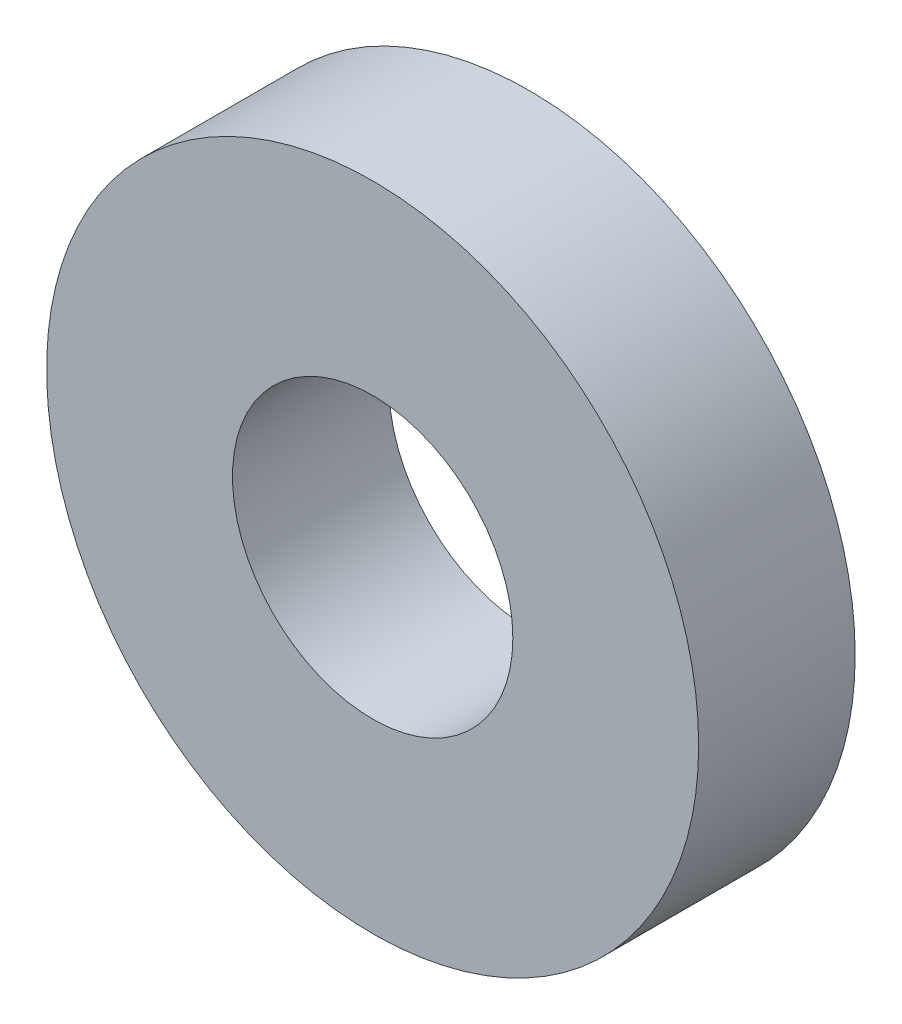
SolidWorks part; units mm, degrees
ref_plane "Front Plane" through (0, 0, 0) normal (0, 0, 1) x (1, 0, 0)
ref_plane "Top Plane" through (0, 0, 0) normal (0, 1, 0) x (1, 0, 0)
ref_plane "Right Plane" through (0, 0, 0) normal (1, 0, 0) x (0, 0, -1)
sketch "Sketch1" plane through (0, 0, 0) normal (0, 0, 1) x (1, 0, 0)
  circle A0 centre (0, 0) radius 5
  circle A1 centre (0, 0) radius 2.15
  dimension "OD" = 10
  dimension "ID1" = 4.3
extrude "Boss-Extrude1" add sketch "Sketch1" along normal blind 2.4
